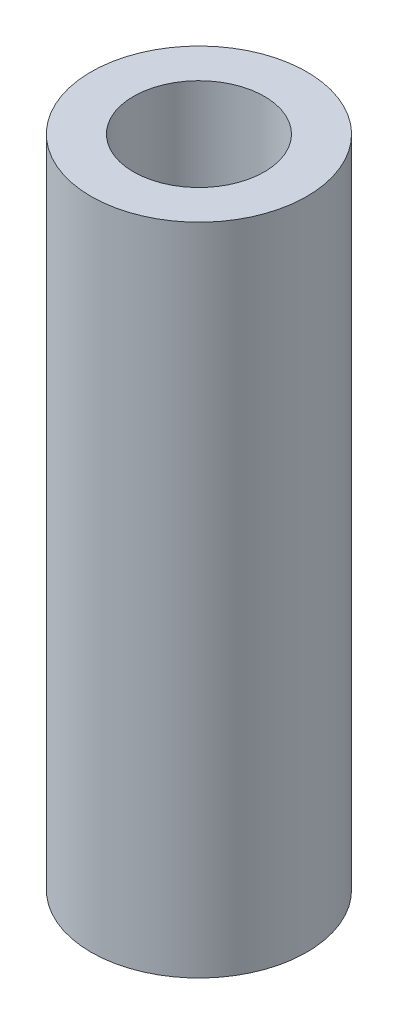
SolidWorks part; units mm, degrees
material "Natural Rubber"
ref_plane "Front Plane" through (0, 0, 0) normal (0, 0, 1) x (1, 0, 0)
ref_plane "Top Plane" through (0, 0, 0) normal (0, 1, 0) x (1, 0, 0)
ref_plane "Right Plane" through (0, 0, 0) normal (1, 0, 0) x (0, 0, -1)
sketch "Sketch2" plane through (0, 0, 0) normal (0, 1, 0) x (1, 0, 0)
  circle A0 centre (0, 0) radius 50.2539
  circle A1 centre (0, 0) radius 30.48
extrude "Boss-Extrude1" add sketch "Sketch2" along normal blind 304.8
